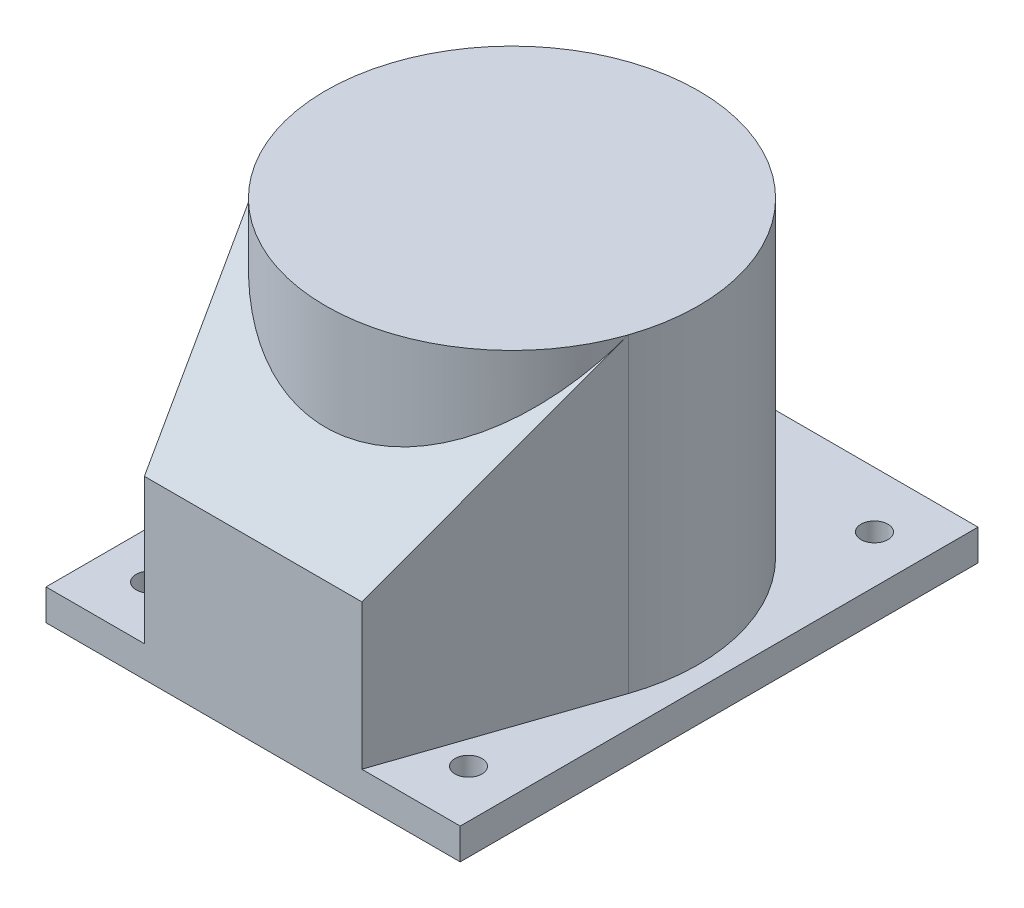
SolidWorks part; units mm, degrees
ref_plane "Front Plane" through (0, 0, 0) normal (0, 0, 1) x (1, 0, 0)
ref_plane "Top Plane" through (0, 0, 0) normal (0, 1, 0) x (1, 0, 0)
ref_plane "Right Plane" through (0, 0, 0) normal (1, 0, 0) x (0, 0, -1)
sketch "Sketch1" plane through (0, 0, 0) normal (0, 1, 0) x (1, 0, 0)
  line L1 (125, 100) -> (-125, 100)
  line L2 (125, 100) -> (125, -100)
  line L3 (125, -100) -> (-125, -100)
  line L4 (-125, 100) -> (-125, -100)
  line L5 (0, -100) -> (0, 100) construction
  line L6 (125, 0) -> (-125, 0) construction
  circle A0 centre (-98, 77) radius 6.5
  circle A1 centre (98, 77) radius 6.5
  circle A2 centre (-98, -77) radius 6.5
  circle A3 centre (98, -77) radius 6.5
  point P0 (0, 0)
  dimension "D3" = 13
  dimension "D1" = 200
  dimension "D2" = 250
  dimension "D4" = 23
  dimension "D5" = 27
extrude "Boss-Extrude1" add sketch "Sketch1" along normal blind 15
sketch "Sketch2" plane through (0, 15, 0) normal (0, 1, 0) x (1, 0, 0)
  line L0 (125, 52.5) -> (29.0188, 85.1934)
  line L1 (125, -100) -> (125, 100) construction
  line L2 (125, 0) -> (165.536, 0) construction
  line L3 (125, -52.5) -> (29.0188, -85.1934)
  line L5 (125, -52.5) -> (125, 52.5)
  arc A0 (29.0188, 85.1934) -> (29.0188, -85.1934) centre (0, 0) ccw
  dimension "D1" = 180
  dimension "D2" = 105
extrude "Boss-Extrude2" add sketch "Sketch2" along normal blind 150 contours L0 A0 L3 L5
sketch "Sketch3" plane through (0, 0, 0) normal (0, 0, 1) x (1, 0, 0)
  line L0 (29.0188, 165) -> (125, 85)
  line L1 (125, 165) -> (125, 15) construction
  line L2 (125, 165) -> (29.0188, 165) construction
  dimension "D1" = 80
extrude "Cut-Extrude1" cut sketch "Sketch3" against normal through all and the other way through all
sketch "Sketch4" plane through (0, 165, 0) normal (0, 1, 0) x (1, 0, 0)
  line L0 (125, -52.5) -> (29.0188, -85.1934) construction
  line L1 (29.0188, -85.1934) -> (29.0188, 85.1934)
  arc A0 (29.0188, 85.1934) -> (29.0188, -85.1934) centre (0, 0) cw
extrude "Boss-Extrude3" add sketch "Sketch4" against normal up to next
move or copy body "Body-Move/Copy1" bodies to move or copy 104 copy no rotation origin (0, 0, 0) rotation axis (0, -1, 0) rotation angle 90
